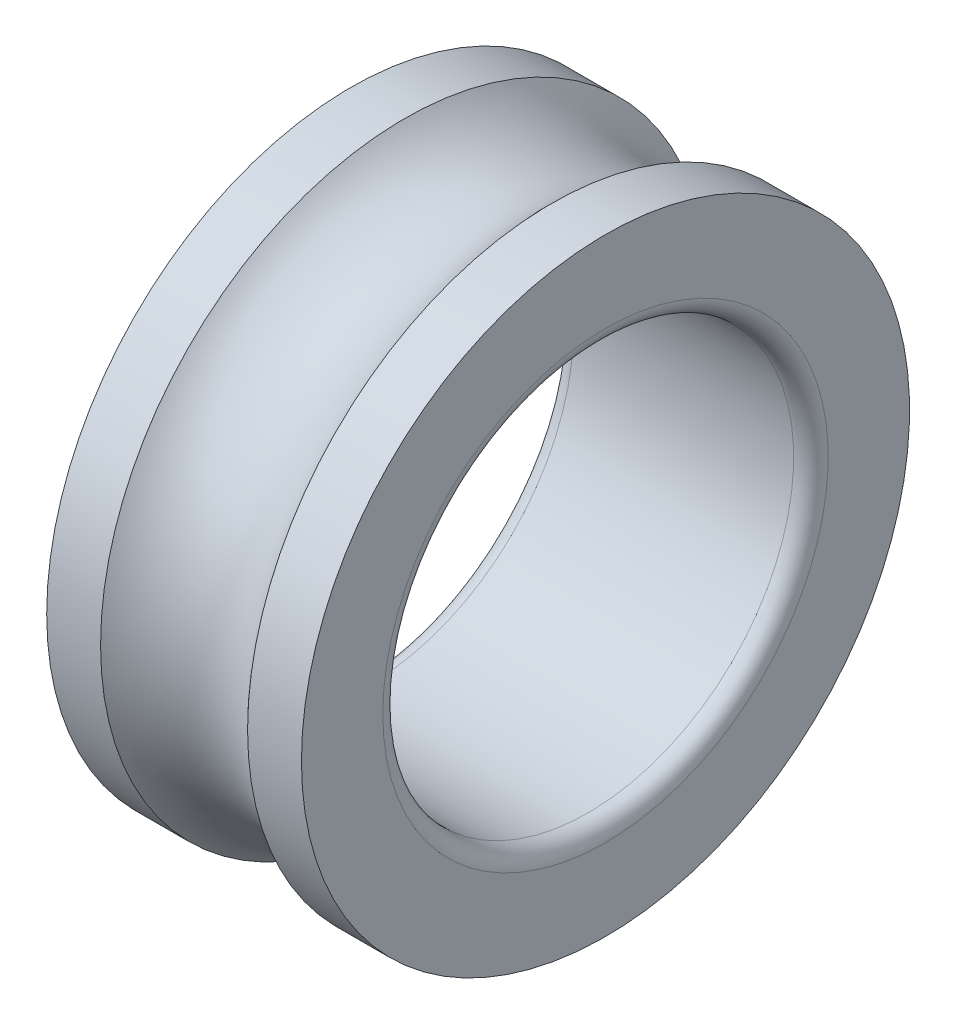
SolidWorks part; units mm, degrees
material "Cast Stainless Steel"
ref_plane "Front Plane" through (0, 0, 0) normal (0, 0, 1) x (1, 0, 0)
ref_plane "Top Plane" through (0, 0, 0) normal (0, 1, 0) x (1, 0, 0)
ref_plane "Right Plane" through (0, 0, 0) normal (1, 0, 0) x (0, 0, -1)
sketch "Sketch1" plane through (0, 0, 0) normal (0, 0, 1) x (1, 0, 0)
  line L0 (-62.7041, 0) -> (94.6062, 0) construction
  line L1 (8.9443, 37) -> (15.5, 37)
  line L2 (-15.5, 37) -> (-8.9443, 37)
  line L3 (-15.5, 37) -> (-15.5, 27.1)
  line L4 (-13.4, 25) -> (13.4, 25)
  line L5 (15.5, 37) -> (15.5, 27.1)
  line L6 (-15.5, 37) -> (15.5, 25) construction
  line L7 (-15.5, 25) -> (15.5, 37) construction
  line L8 (0, 25) -> (0, 0) construction
  arc A0 (8.9443, 37) -> (-8.9443, 37) centre (0, 45) cw
  arc A1 (13.4, 25) -> (15.5, 27.1) centre (13.4, 27.1) ccw
  arc A2 (-15.5, 27.1) -> (-13.4, 25) centre (-13.4, 27.1) ccw
  point P3 (0, 31)
  dimension "D5" = 12
  dimension "D6" = 2.1
  dimension "D1" = 31
  dimension "D2" = 25
  dimension "D3" = 37
  dimension "D4" = 8
revolve "Revolve1" add sketch "Sketch1" angle 360 about L0
